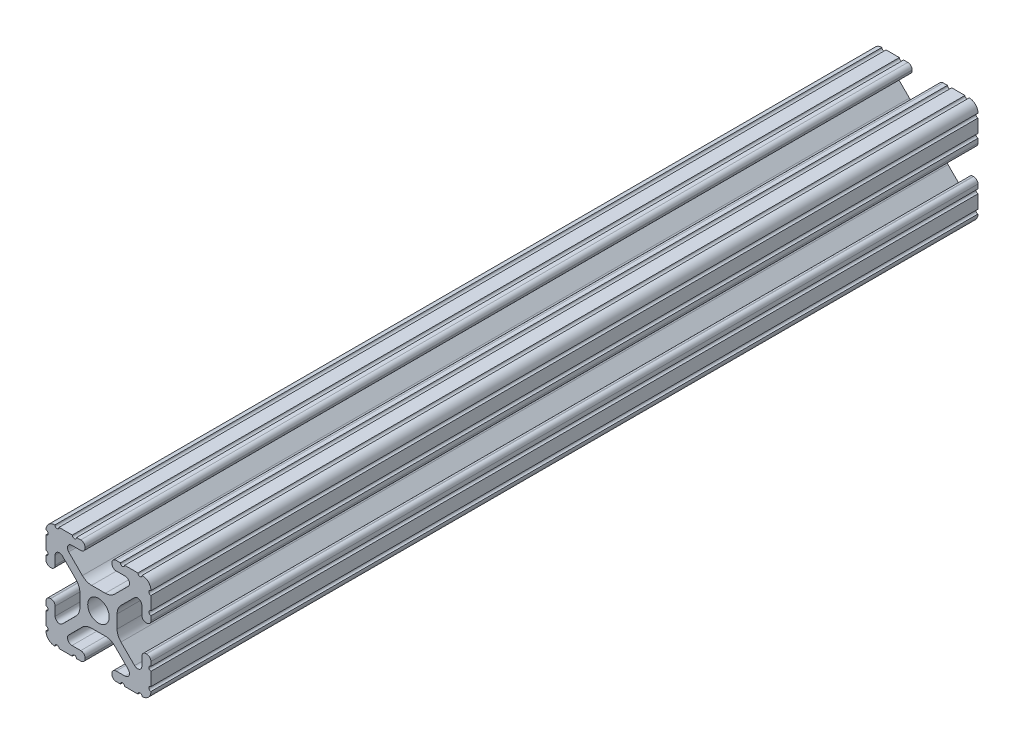
SolidWorks part; units mm, degrees
ref_plane "Front" through (0, 0, 0) normal (0, 0, 1) x (1, 0, 0)
ref_plane "Top" through (0, 0, 0) normal (0, 1, 0) x (1, 0, 0)
ref_plane "Right" through (0, 0, 0) normal (1, 0, 0) x (0, 0, -1)
sketch "Sketch1" plane through (0, 0, 0) normal (0, 0, 1) x (1, 0, 0)
  line L0 (-7.5107, 9.4563) -> (7.5107, 9.4563) construction
  line L1 (-7.4968, -9.4098) -> (7.4968, -9.4098) construction
  line L88 (-7.1797, -8.6452) -> (-3.9523, -5.4237)
  line L89 (-1.7093, -4.4958) -> (1.7093, -4.4958)
  line L90 (3.9523, -5.4237) -> (7.1797, -8.6452)
  line L91 (6.4164, -10.4902) -> (4.2875, -10.4902)
  line L92 (3.2385, -11.5392) -> (3.2385, -11.651)
  line L93 (4.2875, -12.7) -> (5.3171, -12.7)
  line L94 (6.3331, -12.7) -> (9.5504, -12.7)
  line L95 (12.7, -9.5504) -> (12.7, -6.3331)
  line L96 (12.7, -5.3171) -> (12.7, -4.2875)
  line L97 (11.651, -3.2385) -> (11.5392, -3.2385)
  line L98 (10.4902, -4.2875) -> (10.4902, -6.4021)
  line L99 (8.7371, -7.1294) -> (5.441, -3.8408)
  line L100 (4.5085, -1.5932) -> (4.5085, 1.5932)
  line L101 (5.441, 3.8408) -> (8.7371, 7.1294)
  line L102 (10.4902, 6.4021) -> (10.4902, 4.2875)
  line L103 (11.5392, 3.2385) -> (11.651, 3.2385)
  line L104 (12.7, 4.2875) -> (12.7, 5.3171)
  line L105 (12.7, 6.3331) -> (12.7, 9.5504)
  line L106 (9.5504, 12.7) -> (6.3331, 12.7)
  line L107 (5.3171, 12.7) -> (4.2875, 12.7)
  line L108 (3.2385, 11.651) -> (3.2385, 11.5392)
  line L109 (4.2875, 10.4902) -> (6.4768, 10.4902)
  line L110 (7.207, 8.7244) -> (3.8983, 5.4232)
  line L111 (1.6558, 4.4958) -> (-1.6558, 4.4958)
  line L112 (-3.8983, 5.4232) -> (-7.207, 8.7244)
  line L113 (-6.4768, 10.4902) -> (-4.2875, 10.4902)
  line L114 (-3.2385, 11.5392) -> (-3.2385, 11.651)
  line L115 (-4.2875, 12.7) -> (-5.3171, 12.7)
  line L116 (-6.3331, 12.7) -> (-9.5504, 12.7)
  line L117 (-12.7, 9.5504) -> (-12.7, 6.3331)
  line L118 (-12.7, 5.3171) -> (-12.7, 4.2875)
  line L119 (-11.651, 3.2385) -> (-11.5392, 3.2385)
  line L120 (-10.4902, 4.2875) -> (-10.4902, 6.4021)
  line L121 (-8.7371, 7.1294) -> (-5.441, 3.8408)
  line L122 (-4.5085, 1.5932) -> (-4.5085, -1.5932)
  line L123 (-5.441, -3.8408) -> (-8.7371, -7.1294)
  line L124 (-10.4902, -6.4021) -> (-10.4902, -4.2875)
  line L125 (-11.5392, -3.2385) -> (-11.651, -3.2385)
  line L126 (-12.7, -4.2875) -> (-12.7, -5.3171)
  line L127 (-12.7, -6.3331) -> (-12.7, -9.5504)
  line L128 (-9.5504, -12.7) -> (-6.3331, -12.7)
  line L129 (-5.3171, -12.7) -> (-4.2875, -12.7)
  line L130 (-3.2385, -11.651) -> (-3.2385, -11.5392)
  line L131 (-4.2875, -10.4902) -> (-6.4164, -10.4902)
  circle A1 centre (0, 0) radius 2.6035
  arc A104 (-7.1797, -8.6452) -> (-6.4164, -10.4902) centre (-6.4164, -9.4098) ccw
  arc A105 (-1.7093, -4.4958) -> (-3.9523, -5.4237) centre (-1.7093, -7.6708) ccw
  arc A106 (3.9523, -5.4237) -> (1.7093, -4.4958) centre (1.7093, -7.6708) ccw
  arc A107 (6.4164, -10.4902) -> (7.1797, -8.6452) centre (6.4164, -9.4098) ccw
  arc A108 (4.2875, -10.4902) -> (3.2385, -11.5392) centre (4.2875, -11.5392) ccw
  arc A109 (3.2385, -11.651) -> (4.2875, -12.7) centre (4.2875, -11.651) ccw
  arc A110 (6.3331, -12.7) -> (5.3171, -12.7) centre (5.8251, -12.7) ccw
  arc A111 (10.5664, -12.6998) -> (9.5504, -12.7) centre (10.0584, -12.7) ccw
  arc A112 (10.5664, -12.6998) -> (12.6998, -10.5664) centre (10.5918, -10.5918) ccw
  arc A113 (12.7, -9.5504) -> (12.6998, -10.5664) centre (12.7, -10.0584) ccw
  arc A114 (12.7, -5.3171) -> (12.7, -6.3331) centre (12.7, -5.8251) ccw
  arc A115 (12.7, -4.2875) -> (11.651, -3.2385) centre (11.651, -4.2875) ccw
  arc A116 (11.5392, -3.2385) -> (10.4902, -4.2875) centre (11.5392, -4.2875) ccw
  arc A117 (8.7371, -7.1294) -> (10.4902, -6.4021) centre (9.4628, -6.4021) ccw
  arc A118 (4.5085, -1.5932) -> (5.441, -3.8408) centre (7.6835, -1.5932) ccw
  arc A119 (5.441, 3.8408) -> (4.5085, 1.5932) centre (7.6835, 1.5932) ccw
  arc A120 (10.4902, 6.4021) -> (8.7371, 7.1294) centre (9.4628, 6.4021) ccw
  arc A121 (10.4902, 4.2875) -> (11.5392, 3.2385) centre (11.5392, 4.2875) ccw
  arc A122 (11.651, 3.2385) -> (12.7, 4.2875) centre (11.651, 4.2875) ccw
  arc A123 (12.7, 6.3331) -> (12.7, 5.3171) centre (12.7, 5.8251) ccw
  arc A124 (12.6998, 10.5664) -> (12.7, 9.5504) centre (12.7, 10.0584) ccw
  arc A125 (12.6998, 10.5664) -> (10.5664, 12.6998) centre (10.5918, 10.5918) ccw
  arc A126 (9.5504, 12.7) -> (10.5664, 12.6998) centre (10.0584, 12.7) ccw
  arc A127 (5.3171, 12.7) -> (6.3331, 12.7) centre (5.8251, 12.7) ccw
  arc A128 (4.2875, 12.7) -> (3.2385, 11.651) centre (4.2875, 11.651) ccw
  arc A129 (3.2385, 11.5392) -> (4.2875, 10.4902) centre (4.2875, 11.5392) ccw
  arc A130 (7.207, 8.7244) -> (6.4768, 10.4902) centre (6.4768, 9.4563) ccw
  arc A131 (1.6558, 4.4958) -> (3.8983, 5.4232) centre (1.6558, 7.6708) ccw
  arc A132 (-3.8983, 5.4232) -> (-1.6558, 4.4958) centre (-1.6558, 7.6708) ccw
  arc A133 (-6.4768, 10.4902) -> (-7.207, 8.7244) centre (-6.4768, 9.4563) ccw
  arc A134 (-4.2875, 10.4902) -> (-3.2385, 11.5392) centre (-4.2875, 11.5392) ccw
  arc A135 (-3.2385, 11.651) -> (-4.2875, 12.7) centre (-4.2875, 11.651) ccw
  arc A136 (-6.3331, 12.7) -> (-5.3171, 12.7) centre (-5.8251, 12.7) ccw
  arc A137 (-10.5664, 12.6998) -> (-9.5504, 12.7) centre (-10.0584, 12.7) ccw
  arc A138 (-10.5664, 12.6998) -> (-12.6998, 10.5664) centre (-10.5918, 10.5918) ccw
  arc A139 (-12.7, 9.5504) -> (-12.6998, 10.5664) centre (-12.7, 10.0584) ccw
  arc A140 (-12.7, 5.3171) -> (-12.7, 6.3331) centre (-12.7, 5.8251) ccw
  arc A141 (-12.7, 4.2875) -> (-11.651, 3.2385) centre (-11.651, 4.2875) ccw
  arc A142 (-11.5392, 3.2385) -> (-10.4902, 4.2875) centre (-11.5392, 4.2875) ccw
  arc A143 (-8.7371, 7.1294) -> (-10.4902, 6.4021) centre (-9.4628, 6.4021) ccw
  arc A144 (-4.5085, 1.5932) -> (-5.441, 3.8408) centre (-7.6835, 1.5932) ccw
  arc A145 (-5.441, -3.8408) -> (-4.5085, -1.5932) centre (-7.6835, -1.5932) ccw
  arc A146 (-10.4902, -6.4021) -> (-8.7371, -7.1294) centre (-9.4628, -6.4021) ccw
  arc A147 (-10.4902, -4.2875) -> (-11.5392, -3.2385) centre (-11.5392, -4.2875) ccw
  arc A148 (-11.651, -3.2385) -> (-12.7, -4.2875) centre (-11.651, -4.2875) ccw
  arc A149 (-12.7, -6.3331) -> (-12.7, -5.3171) centre (-12.7, -5.8251) ccw
  arc A150 (-12.6998, -10.5664) -> (-12.7, -9.5504) centre (-12.7, -10.0584) ccw
  arc A151 (-12.6998, -10.5664) -> (-10.5664, -12.6998) centre (-10.5918, -10.5918) ccw
  arc A152 (-9.5504, -12.7) -> (-10.5664, -12.6998) centre (-10.0584, -12.7) ccw
  arc A153 (-5.3171, -12.7) -> (-6.3331, -12.7) centre (-5.8251, -12.7) ccw
  arc A154 (-4.2875, -12.7) -> (-3.2385, -11.651) centre (-4.2875, -11.651) ccw
  arc A155 (-3.2385, -11.5392) -> (-4.2875, -10.4902) centre (-4.2875, -11.5392) ccw
extrude "Boss-Extrude1" add sketch "Sketch1" along normal mid plane 914.4
sketch "Sketch3" plane through (-12.7, 0, 0) normal (-1, 0, 0) x (0, 0, 1)
  line L2 (-203.2, 21.063) -> (-461.0909, 21.063)
  line L3 (-461.0909, 21.063) -> (-461.0909, -25.4)
  line L4 (-461.0909, -25.4) -> (-203.2, -27.2496)
  line L5 (-203.2, 21.063) -> (257.0298, 21.063)
  line L6 (257.0298, 21.063) -> (257.0298, -27.2496)
  line L7 (-203.2, -27.2496) -> (257.0298, -27.2496)
extrude "Cut-Extrude2" cut sketch "Sketch3" against normal blind 26.924 and the other way blind 4.318
